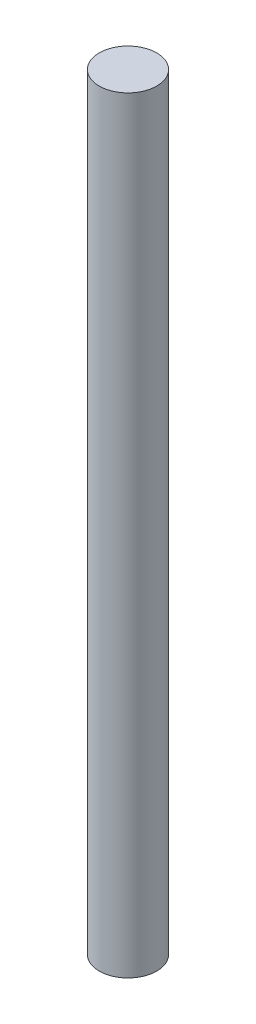
SolidWorks part; units mm, degrees
ref_plane "Front Plane" through (0, 0, 0) normal (0, 0, 1) x (1, 0, 0)
ref_plane "Top Plane" through (0, 0, 0) normal (0, 1, 0) x (1, 0, 0)
ref_plane "Right Plane" through (0, 0, 0) normal (1, 0, 0) x (0, 0, -1)
sketch "Sketch1" plane through (0, 0, 0) normal (0, 1, 0) x (1, 0, 0)
  circle A0 centre (0, 0) radius 0.75
  dimension "D1" = 1.5
extrude "Boss-Extrude1" add sketch "Sketch1" along normal blind 20
